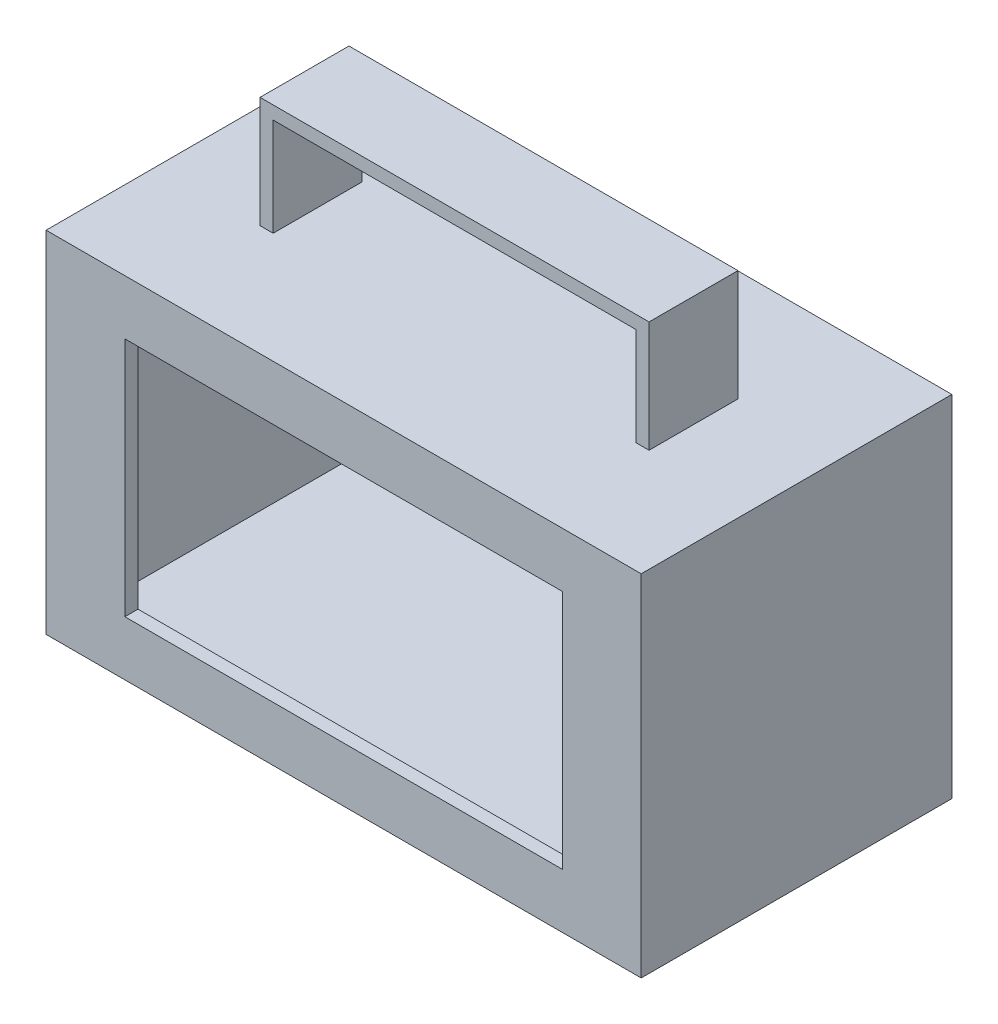
SolidWorks part; units mm, degrees
ref_plane "Front Plane" through (0, 0, 0) normal (0, 0, 1) x (1, 0, 0)
ref_plane "Top Plane" through (0, 0, 0) normal (0, 1, 0) x (1, 0, 0)
ref_plane "Right Plane" through (0, 0, 0) normal (1, 0, 0) x (0, 0, -1)
sketch "Sketch1" plane through (0, 0, 0) normal (0, 1, 0) x (1, 0, 0)
  line L0 (-68, 35.5) -> (-68, -35.5)
  line L1 (-65, 32.5) -> (65, 32.5) construction
  line L2 (-65, 32.5) -> (-65, -32.5) construction
  line L3 (-65, -32.5) -> (65, -32.5) construction
  line L4 (65, 32.5) -> (65, -32.5) construction
  line L5 (-65, 32.5) -> (65, -32.5) construction
  line L6 (-65, -32.5) -> (65, 32.5) construction
  line L7 (-68, -35.5) -> (68, -35.5)
  line L8 (68, 35.5) -> (68, -35.5)
  line L9 (-68, 35.5) -> (68, 35.5)
  point P0 (0, 0)
  dimension "D1" = 130
  dimension "D2" = 65
  dimension "D3" = 3
extrude "Boss-Extrude2" add sketch "Sketch1" along normal blind 80
shell "Shell5" thickness 3
sketch "Sketch2" plane through (0, 3, 0) normal (0, 1, 0) x (1, 0, 0)
  line L0 (-65, -35.5) -> (65, -35.5) construction
  line L1 (-65, -35.5) -> (65, -35.5)
  line L2 (-65, -32.5) -> (65, -32.5)
  line L3 (-65, -35.5) -> (-65, -32.5)
  line L5 (65, -35.5) -> (65, -32.5)
  dimension "D1" = 3
extrude "Boss-Extrude3" add sketch "Sketch2" along normal up to surface (74 mm away) up to face at (0, 77, 1.5)
sketch "Sketch4" plane through (0, 0, 0) normal (0, 0, 1) x (1, 0, 0)
  line L0 (-68, 80) -> (68, 80) construction
  line L1 (-44.45, 80) -> (44.45, 80) construction
  line L2 (-44.45, 80) -> (-44.45, 105.4)
  line L3 (-44.45, 105.4) -> (44.45, 105.4)
  line L4 (44.45, 80) -> (44.45, 105.4)
  line L5 (0, 0) -> (0, 80) construction
  line L6 (-41.45, 80) -> (-41.45, 102.4)
  line L7 (-41.45, 102.4) -> (41.45, 102.4)
  line L8 (41.45, 80) -> (41.45, 102.4)
  line L9 (-41.45, 80) -> (-44.45, 80)
  line L10 (41.45, 80) -> (44.45, 80)
  dimension "D1" = 88.9
  dimension "D2" = 25.4
  dimension "D3" = 3
extrude "Boss-Extrude4" add sketch "Sketch4" along normal mid plane 20.32
sketch "Sketch6" plane through (0, 0, 35.5) normal (0, 0, 1) x (1, 0, 0)
  line L0 (-68, 0) -> (68, 0) construction
  line L1 (-68, 80) -> (-68, 0) construction
  line L2 (-68, 80) -> (68, 80) construction
  line L3 (68, 80) -> (68, 0) construction
  line L4 (-68, 0) -> (68, 0)
  line L5 (-68, 80) -> (-68, 0)
  line L6 (-68, 80) -> (68, 80)
  line L7 (68, 80) -> (68, 0)
sketch "Sketch7" plane through (0, 0, 35.5) normal (0, 0, 1) x (1, 0, 0)
  line L0 (-68, 0) -> (68, 0) construction
  line L1 (-50, 67.5) -> (50, 67.5)
  line L2 (-50, 67.5) -> (-50, 12.5)
  line L3 (-50, 12.5) -> (50, 12.5)
  line L4 (50, 67.5) -> (50, 12.5)
  line L5 (-50, 67.5) -> (50, 12.5) construction
  line L6 (-50, 12.5) -> (50, 67.5) construction
  point P0 (0, 40)
  point P5 (0, 0)
  dimension "D1" = 55
  dimension "D2" = 100
  dimension "D3" = 40
extrude "Cut-Extrude1" cut sketch "Sketch7" against normal blind 10
sketch "Sketch8" plane through (0, 0, -35.5) normal (0, 0, -1) x (-1, 0, 0)
  line L1 (-56.325, 21.23) -> (53.675, 21.23)
  line L2 (-56.325, 21.23) -> (-56.325, 61.23)
  line L3 (-56.325, 61.23) -> (53.675, 61.23)
  line L4 (53.675, 21.23) -> (53.675, 61.23)
  dimension "D1" = 110
  dimension "D2" = 40
extrude "Cut-Extrude2" cut sketch "Sketch8" against normal blind 10
